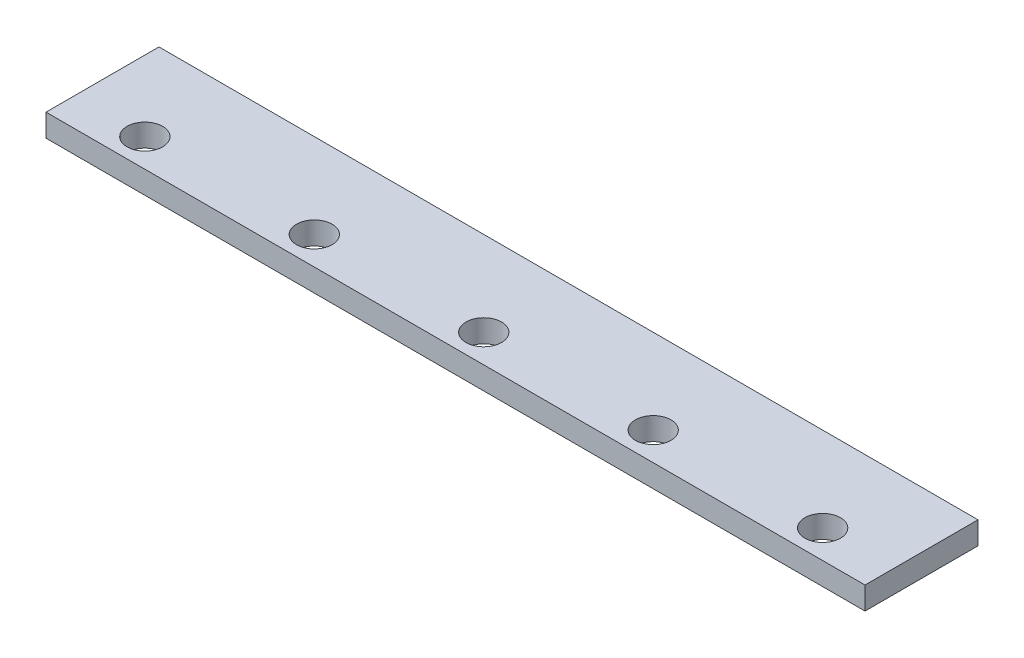
SolidWorks part; units mm, degrees
ref_plane "Front Plane" through (0, 0, 0) normal (0, 0, 1) x (1, 0, 0)
ref_plane "Top Plane" through (0, 0, 0) normal (0, 1, 0) x (1, 0, 0)
ref_plane "Right Plane" through (0, 0, 0) normal (1, 0, 0) x (0, 0, -1)
sketch "Sketch1" plane through (0, 0, 0) normal (0, 1, 0) x (1, 0, 0)
  line L0 (0, 0) -> (580, 0)
  line L1 (580, 0) -> (580, 80)
  line L2 (580, 80) -> (0, 80)
  line L3 (0, 80) -> (0, 0)
  circle A0 centre (50, 20) radius 12.6
  circle A1 centre (170, 20) radius 12.6
  circle A2 centre (290, 20) radius 12.6
  circle A3 centre (410, 20) radius 12.6
  circle A4 centre (530, 20) radius 12.6
  dimension "D3" = 25.2
  dimension "D1" = 580
  dimension "D2" = 80
  dimension "D4" = 20
  dimension "D5" = 50
  dimension "D7" = 120
  dimension "D6" = 5
extrude "Boss-Extrude1" add sketch "Sketch1" along normal blind 16
